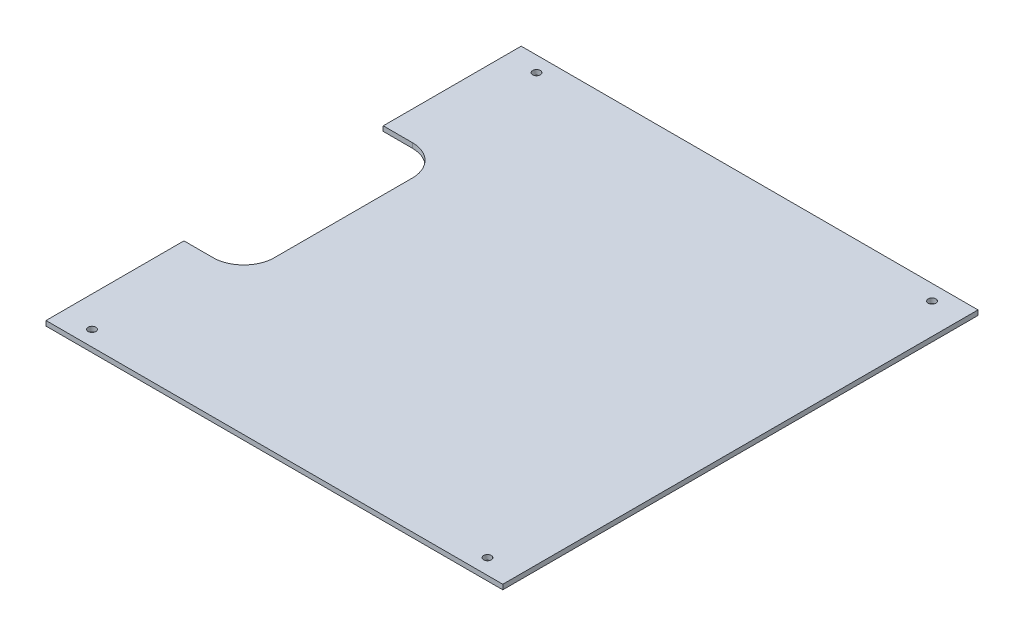
SolidWorks part; units mm, degrees
ref_plane "Front Plane" through (0, 0, 0) normal (0, 0, 1) x (1, 0, 0)
ref_plane "Top Plane" through (0, 0, 0) normal (0, 1, 0) x (1, 0, 0)
ref_plane "Right Plane" through (0, 0, 0) normal (1, 0, 0) x (0, 0, -1)
sketch "Sketch2" plane through (0, 0, 0) normal (0, 1, 0) x (1, 0, 0)
  line L0 (0, 289) -> (21, 289)
  line L2 (0, 289) -> (0, 220)
  line L3 (21, 0) -> (319, 0)
  line L4 (340, 289) -> (340, 21)
  line L5 (21, 289) -> (21, 310)
  line L6 (21, 310) -> (319, 310)
  line L7 (21, 0) -> (21, 21)
  line L10 (340, 21) -> (319, 21)
  line L11 (21, 21) -> (0, 21)
  line L12 (319, 21) -> (319, 0)
  line L13 (0, 90) -> (0, 21)
  line L14 (0, 220) -> (40, 220)
  line L18 (319, 310) -> (319, 289)
  line L19 (60, 200) -> (60, 110)
  line L20 (40, 90) -> (0, 90)
  line L21 (319, 289) -> (340, 289)
  line L22 (319, 289) -> (319, 21)
  line L23 (21, 289) -> (21, 21)
  arc A6 (60, 110) -> (40, 90) centre (40, 110) cw
  arc A7 (40, 220) -> (60, 200) centre (40, 200) cw
  dimension "D6" = 21
  dimension "D7" = 21
  dimension "D16" = 20
  dimension "D1" = 340
  dimension "D2" = 90
  dimension "D3" = 21
  dimension "D4" = 21
  dimension "D5" = 21
  dimension "D8" = 60
  dimension "D9" = 310
  dimension "D12" = 21
  dimension "D13" = 21
  dimension "D14" = 90
extrude "Boss-Extrude1" add sketch "Sketch2" along normal blind 3.175
sketch "Sketch3" plane through (0, 3.175, 0) normal (0, 1, 0) x (1, 0, 0)
  line L1 (0, 289) -> (0, 220) construction
  line L2 (21, 220) -> (21, 310) construction
  line L3 (0, 289) -> (21, 289) construction
  line L4 (21, 0) -> (319, 0) construction
  line L5 (21, 21) -> (0, 21) construction
  line L6 (21, 0) -> (21, 90) construction
  line L7 (319, 310) -> (319, 0) construction
  line L8 (340, 21) -> (319, 21) construction
  line L9 (340, 289) -> (340, 21) construction
  line L10 (21, 310) -> (319, 310) construction
  line L13 (21, 310) -> (319, 310) construction
  line L14 (319, 310) -> (319, 0) construction
  line L15 (319, 289) -> (340, 289) construction
  circle A0 centre (41, 300) radius 2.5
  circle A2 centre (10, 269) radius 2.5
  circle A3 centre (299, 300) radius 2.5
  circle A4 centre (330, 269) radius 2.5
  circle A5 centre (330, 41) radius 2.5
  circle A6 centre (299, 10) radius 2.5
  circle A7 centre (41, 10) radius 2.5
  circle A8 centre (10, 41) radius 2.5
  dimension "D3" = 5
  dimension "D4" = 5
  dimension "D7" = 5
  dimension "D8" = 5
  dimension "D9" = 5
  dimension "D10" = 5
  dimension "D19" = 5
  dimension "D20" = 5
  dimension "D21" = 10
  dimension "D22" = 10
  dimension "D23" = 20
  dimension "D24" = 20
  dimension "D2" = 10
  dimension "D5" = 20
  dimension "D6" = 20
  dimension "D11" = 10
  dimension "D12" = 10
  dimension "D13" = 10
  dimension "D14" = 20
  dimension "D15" = 20
  dimension "D16" = 20
  dimension "D17" = 20
  dimension "D18" = 10
  dimension "D25" = 10
extrude "Cut-Extrude1" cut sketch "Sketch3" against normal blind 10
